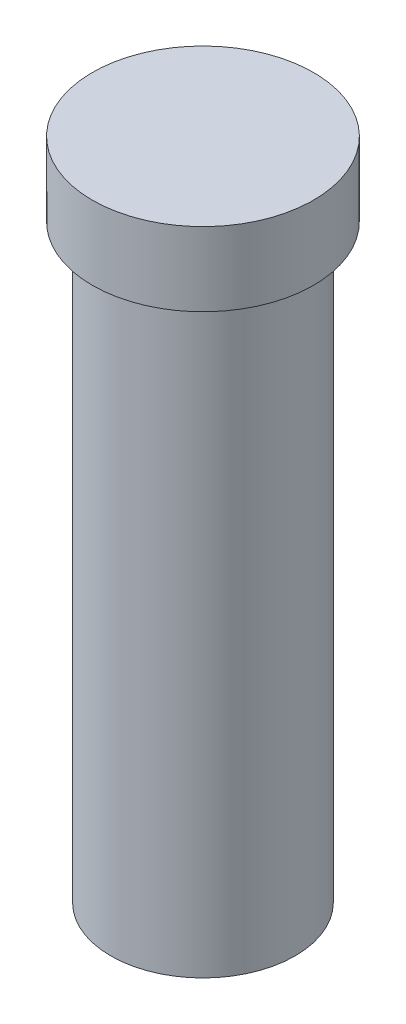
SolidWorks part; units mm, degrees
ref_plane "Alzado" through (0, 0, 0) normal (0, 0, 1) x (1, 0, 0)
ref_plane "Planta" through (0, 0, 0) normal (0, 1, 0) x (1, 0, 0)
ref_plane "Vista lateral" through (0, 0, 0) normal (1, 0, 0) x (0, 0, -1)
sketch "Croquis1" plane through (0, 0, 0) normal (0, 1, 0) x (1, 0, 0)
  circle A0 centre (0, 0) radius 12.5
  dimension "D1" = 25
extrude "Saliente-Extruir1" add sketch "Croquis1" along normal mid plane 90
sketch "Croquis2" plane through (0, 45, 0) normal (0, 1, 0) x (1, 0, 0)
  circle A0 centre (0, 0) radius 15
  dimension "D1" = 30
extrude "Saliente-Extruir2" add sketch "Croquis2" against normal blind 10
